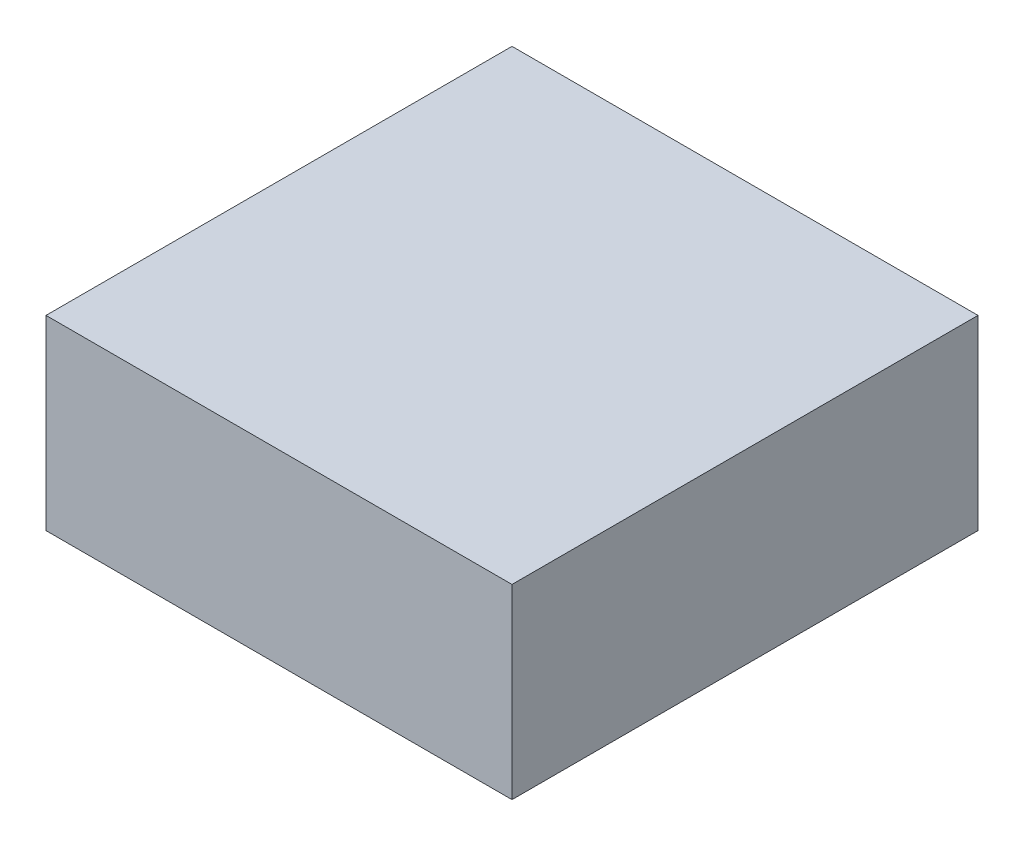
SolidWorks part; units mm, degrees
ref_plane "Front Plane" through (0, 0, 0) normal (0, 0, 1) x (1, 0, 0)
ref_plane "Top Plane" through (0, 0, 0) normal (0, 1, 0) x (1, 0, 0)
ref_plane "Right Plane" through (0, 0, 0) normal (1, 0, 0) x (0, 0, -1)
sketch "Sketch1" plane through (0, 0, 0) normal (0, 1, 0) x (1, 0, 0)
  line L1 (-63.5, -63.5) -> (63.5, -63.5)
  line L2 (-63.5, -63.5) -> (-63.5, 63.5)
  line L3 (-63.5, 63.5) -> (63.5, 63.5)
  line L4 (63.5, -63.5) -> (63.5, 63.5)
  line L5 (-63.5, -63.5) -> (63.5, 63.5) construction
  line L6 (-63.5, 63.5) -> (63.5, -63.5) construction
  point P0 (0, 0)
  dimension "D1" = 127
  dimension "D2" = 127
extrude "Boss-Extrude1" add sketch "Sketch1" along normal blind 50.8
